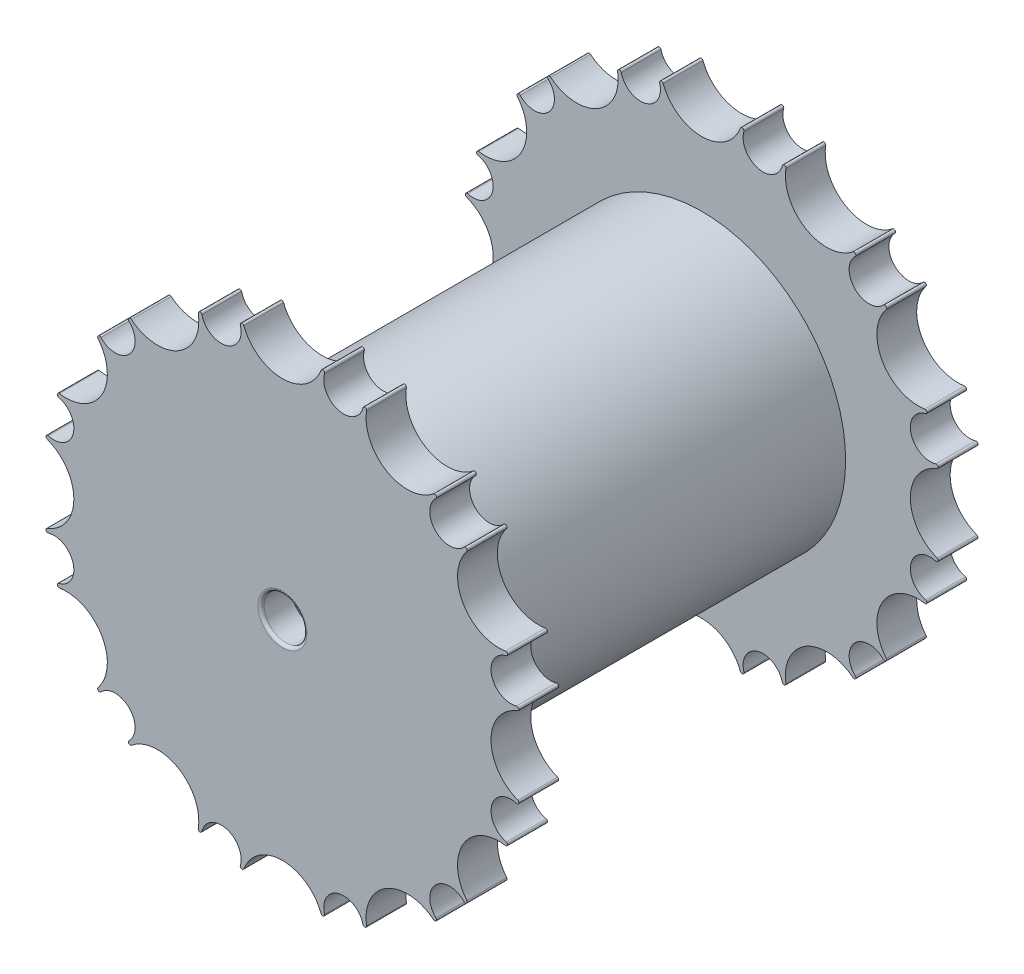
SolidWorks part; units mm, degrees
ref_plane "Front Plane" through (0, 0, 0) normal (0, 0, 1) x (1, 0, 0)
ref_plane "Top Plane" through (0, 0, 0) normal (0, 1, 0) x (1, 0, 0)
ref_plane "Right Plane" through (0, 0, 0) normal (1, 0, 0) x (0, 0, -1)
sketch "Sketch1" plane through (0, 0, 0) normal (0, 0, 1) x (1, 0, 0)
  line L1 (5, -18.6603) -> (13.6603, -13.6603)
  line L2 (13.6603, -13.6603) -> (18.6603, -5)
  line L3 (18.6603, -5) -> (18.6603, 5)
  line L4 (18.6603, 5) -> (13.6603, 13.6603)
  line L5 (13.6603, 13.6603) -> (5, 18.6603)
  line L6 (5, 18.6603) -> (-5, 18.6603)
  line L7 (-5, 18.6603) -> (-13.6603, 13.6603)
  line L8 (-13.6603, 13.6603) -> (-18.6603, 5)
  line L9 (-18.6603, 5) -> (-18.6603, -5)
  line L10 (-18.6603, -5) -> (-13.6603, -13.6603)
  line L11 (-13.6603, -13.6603) -> (-5, -18.6603)
  line L12 (-5, -18.6603) -> (5, -18.6603)
  circle A0 centre (0, 0) radius 18.6603 construction
  circle A1 centre (-5, 18.6603) radius 1.5 construction
  circle A2 centre (5, 18.6603) radius 1.5 construction
  circle A3 centre (-5, 18.6603) radius 1.625
  circle A4 centre (5, 18.6603) radius 1.625
  circle A5 centre (0, 20.4103) radius 3.375 construction
  arc A6 (-3.4408, 19.1179) -> (-3.1557, 19.2136) centre (-3.2964, 19.1603) cw
  arc A7 (3.1557, 19.2136) -> (3.4408, 19.1179) centre (3.2964, 19.1603) cw
  point P1 (0, 18.6603)
  dimension "D2" = 3
  dimension "D5" = 6.75
  dimension "D1" = 10
  dimension "D6" = 1.75
  dimension "D7" = 0.5
  dimension "D3" = 0.125
  dimension "D4" = 0.125
sketch "Sketch10" plane through (0, 0, 0) normal (0, 0, 1) x (1, 0, 0)
  line L2 (-5, -18.6603) -> (5, -18.6603) construction
  line L14 (-3.375, -18.6603) -> (-2.8858, -18.6603)
  circle A0 centre (5, 18.6603) radius 1.625 construction
  arc A1 (3.4408, 19.1179) -> (3.1557, 19.2136) centre (3.2964, 19.1603) ccw construction
  circle A2 centre (0, 20.4103) radius 3.375 construction
  arc A3 (-3.1557, 19.2136) -> (-3.4408, 19.1179) centre (-3.2964, 19.1603) ccw construction
  circle A4 centre (-5, 18.6603) radius 1.625 construction
  arc A5 (3.4408, 19.1179) -> (6.5791, 18.277) centre (5, 18.6603) ccw
  arc A6 (3.4408, 19.1179) -> (3.1557, 19.2136) centre (3.2964, 19.1603) ccw
  arc A7 (-3.1557, 19.2136) -> (3.1557, 19.2136) centre (0, 20.4103) ccw
  arc A8 (-3.1557, 19.2136) -> (-3.4408, 19.1179) centre (-3.2964, 19.1603) ccw
  arc A9 (-6.4073, 17.8478) -> (-3.4408, 19.1179) centre (-5, 18.6603) ccw
  circle A12 centre (0, 0) radius 12.5
  arc A14 (3.375, 18.6603) -> (6.5791, 18.277) centre (5, 18.6603) ccw
  arc A15 (6.8739, 18.2173) -> (6.5791, 18.277) centre (6.7254, 18.2415) ccw
  arc A16 (6.8739, 18.2173) -> (12.3397, 15.0616) centre (10.2051, 17.6758) ccw
  arc A17 (12.5387, 14.8362) -> (12.3397, 15.0616) centre (12.4349, 14.9451) ccw
  arc A18 (12.5387, 14.8362) -> (14.8362, 12.5387) centre (13.6603, 13.6603) ccw
  arc A19 (12.253, 14.4728) -> (14.8362, 12.5387) centre (13.6603, 13.6603) ccw
  arc A20 (15.0616, 12.3397) -> (14.8362, 12.5387) centre (14.9451, 12.4349) ccw
  arc A21 (15.0616, 12.3397) -> (18.2173, 6.8739) centre (17.6758, 10.2051) ccw
  arc A22 (18.277, 6.5791) -> (18.2173, 6.8739) centre (18.2415, 6.7254) ccw
  arc A23 (18.277, 6.5791) -> (19.1179, 3.4408) centre (18.6603, 5) ccw
  arc A24 (17.8478, 6.4073) -> (19.1179, 3.4408) centre (18.6603, 5) ccw
  arc A25 (19.2136, 3.1557) -> (19.1179, 3.4408) centre (19.1603, 3.2964) ccw
  arc A26 (19.2136, 3.1557) -> (19.2136, -3.1557) centre (20.4103, 0) ccw
  arc A27 (19.1179, -3.4408) -> (19.2136, -3.1557) centre (19.1603, -3.2964) ccw
  arc A28 (19.1179, -3.4408) -> (18.277, -6.5791) centre (18.6603, -5) ccw
  arc A29 (18.6603, -3.375) -> (18.277, -6.5791) centre (18.6603, -5) ccw
  arc A30 (18.2173, -6.8739) -> (18.277, -6.5791) centre (18.2415, -6.7254) ccw
  arc A31 (18.2173, -6.8739) -> (15.0616, -12.3397) centre (17.6758, -10.2051) ccw
  arc A32 (14.8362, -12.5387) -> (15.0616, -12.3397) centre (14.9451, -12.4349) ccw
  arc A33 (14.8362, -12.5387) -> (12.5387, -14.8362) centre (13.6603, -13.6603) ccw
  arc A34 (14.4728, -12.253) -> (12.5387, -14.8362) centre (13.6603, -13.6603) ccw
  arc A35 (12.3397, -15.0616) -> (12.5387, -14.8362) centre (12.4349, -14.9451) ccw
  arc A36 (12.3397, -15.0616) -> (6.8739, -18.2173) centre (10.2051, -17.6758) ccw
  arc A37 (6.5791, -18.277) -> (6.8739, -18.2173) centre (6.7254, -18.2415) ccw
  arc A38 (6.5791, -18.277) -> (3.4408, -19.1179) centre (5, -18.6603) ccw
  arc A39 (6.4073, -17.8478) -> (3.4408, -19.1179) centre (5, -18.6603) ccw
  arc A40 (3.1557, -19.2136) -> (3.4408, -19.1179) centre (3.2964, -19.1603) ccw
  arc A41 (3.1557, -19.2136) -> (-3.1557, -19.2136) centre (0, -20.4103) ccw
  arc A42 (-3.4408, -19.1179) -> (-3.1557, -19.2136) centre (-3.2964, -19.1603) ccw
  arc A43 (-3.4408, -19.1179) -> (-6.5791, -18.277) centre (-5, -18.6603) ccw
  arc A44 (-3.375, -18.6603) -> (-6.5791, -18.277) centre (-5, -18.6603) ccw
  arc A45 (-6.8739, -18.2173) -> (-6.5791, -18.277) centre (-6.7254, -18.2415) ccw
  arc A46 (-6.8739, -18.2173) -> (-12.3397, -15.0616) centre (-10.2051, -17.6758) ccw
  arc A47 (-12.5387, -14.8362) -> (-12.3397, -15.0616) centre (-12.4349, -14.9451) ccw
  arc A48 (-12.5387, -14.8362) -> (-14.8362, -12.5387) centre (-13.6603, -13.6603) ccw
  arc A49 (-12.253, -14.4728) -> (-14.8362, -12.5387) centre (-13.6603, -13.6603) ccw
  arc A50 (-15.0616, -12.3397) -> (-14.8362, -12.5387) centre (-14.9451, -12.4349) ccw
  arc A51 (-15.0616, -12.3397) -> (-18.2173, -6.8739) centre (-17.6758, -10.2051) ccw
  arc A52 (-18.277, -6.5791) -> (-18.2173, -6.8739) centre (-18.2415, -6.7254) ccw
  arc A53 (-18.277, -6.5791) -> (-19.1179, -3.4408) centre (-18.6603, -5) ccw
  arc A54 (-17.8478, -6.4073) -> (-19.1179, -3.4408) centre (-18.6603, -5) ccw
  arc A55 (-19.2136, -3.1557) -> (-19.1179, -3.4408) centre (-19.1603, -3.2964) ccw
  arc A56 (-19.2136, -3.1557) -> (-19.2136, 3.1557) centre (-20.4103, 0) ccw
  arc A57 (-19.1179, 3.4408) -> (-19.2136, 3.1557) centre (-19.1603, 3.2964) ccw
  arc A58 (-19.1179, 3.4408) -> (-18.277, 6.5791) centre (-18.6603, 5) ccw
  arc A59 (-18.6603, 3.375) -> (-18.277, 6.5791) centre (-18.6603, 5) ccw
  arc A60 (-18.2173, 6.8739) -> (-18.277, 6.5791) centre (-18.2415, 6.7254) ccw
  arc A61 (-18.2173, 6.8739) -> (-15.0616, 12.3397) centre (-17.6758, 10.2051) ccw
  arc A62 (-14.8362, 12.5387) -> (-15.0616, 12.3397) centre (-14.9451, 12.4349) ccw
  arc A63 (-14.8362, 12.5387) -> (-12.5387, 14.8362) centre (-13.6603, 13.6603) ccw
  arc A64 (-14.4728, 12.253) -> (-12.5387, 14.8362) centre (-13.6603, 13.6603) ccw
  arc A65 (-12.3397, 15.0616) -> (-12.5387, 14.8362) centre (-12.4349, 14.9451) ccw
  arc A66 (-12.3397, 15.0616) -> (-6.8739, 18.2173) centre (-10.2051, 17.6758) ccw
  arc A67 (-6.5791, 18.277) -> (-6.8739, 18.2173) centre (-6.7254, 18.2415) ccw
  arc A68 (-6.5791, 18.277) -> (-3.4408, 19.1179) centre (-5, 18.6603) ccw
  point P162 (0, 0)
  dimension "D2" = 25
  dimension "D1" = 12
sketch "Sketch2" plane through (0, 0, 0) normal (0, 0, 1) x (1, 0, 0)
  line L0 (-10, 37.3205) -> (0, 0) construction
  line L1 (0, 0) -> (10, 37.3205) construction
  arc A5 (6.8815, 38.2358) -> (6.3115, 38.4272) centre (6.5928, 38.3205) ccw
  arc A6 (6.8815, 38.2358) -> (9.1588, 34.1812) centre (10, 37.3205) ccw
  arc A7 (-6.3115, 38.4272) -> (6.3115, 38.4272) centre (0, 40.8205) ccw
  arc A8 (-6.3115, 38.4272) -> (-6.8815, 38.2358) centre (-6.5928, 38.3205) ccw
  arc A9 (-9.1588, 34.1812) -> (-6.8815, 38.2358) centre (-10, 37.3205) ccw
  arc A10 (9.1588, 34.1812) -> (13.1583, 36.5539) centre (10, 37.3205) ccw
  arc A11 (13.7477, 36.4347) -> (13.1583, 36.5539) centre (13.4507, 36.4829) ccw
  arc A12 (13.7477, 36.4347) -> (24.6795, 30.1232) centre (20.4103, 35.3516) ccw
  arc A13 (25.0775, 29.6724) -> (24.6795, 30.1232) centre (24.8698, 29.8901) ccw
  arc A14 (25.0775, 29.6724) -> (25.0224, 25.0224) centre (27.3205, 27.3205) ccw
  arc A15 (25.0224, 25.0224) -> (29.6724, 25.0775) centre (27.3205, 27.3205) ccw
  arc A16 (30.1232, 24.6795) -> (29.6724, 25.0775) centre (29.8901, 24.8698) ccw
  arc A17 (30.1232, 24.6795) -> (36.4347, 13.7477) centre (35.3516, 20.4103) ccw
  arc A18 (36.5539, 13.1583) -> (36.4347, 13.7477) centre (36.4829, 13.4507) ccw
  arc A19 (36.5539, 13.1583) -> (34.1812, 9.1588) centre (37.3205, 10) ccw
  arc A20 (34.1812, 9.1588) -> (38.2358, 6.8815) centre (37.3205, 10) ccw
  arc A21 (38.4272, 6.3115) -> (38.2358, 6.8815) centre (38.3205, 6.5928) ccw
  arc A22 (38.4272, 6.3115) -> (38.4272, -6.3115) centre (40.8205, 0) ccw
  arc A23 (38.2358, -6.8815) -> (38.4272, -6.3115) centre (38.3205, -6.5928) ccw
  arc A24 (38.2358, -6.8815) -> (34.1812, -9.1588) centre (37.3205, -10) ccw
  arc A25 (34.1812, -9.1588) -> (36.5539, -13.1583) centre (37.3205, -10) ccw
  arc A26 (36.4347, -13.7477) -> (36.5539, -13.1583) centre (36.4829, -13.4507) ccw
  arc A27 (36.4347, -13.7477) -> (30.1232, -24.6795) centre (35.3516, -20.4103) ccw
  arc A28 (29.6724, -25.0775) -> (30.1232, -24.6795) centre (29.8901, -24.8698) ccw
  arc A29 (29.6724, -25.0775) -> (25.0224, -25.0224) centre (27.3205, -27.3205) ccw
  arc A30 (25.0224, -25.0224) -> (25.0775, -29.6724) centre (27.3205, -27.3205) ccw
  arc A31 (24.6795, -30.1232) -> (25.0775, -29.6724) centre (24.8698, -29.8901) ccw
  arc A32 (24.6795, -30.1232) -> (13.7477, -36.4347) centre (20.4103, -35.3516) ccw
  arc A33 (13.1583, -36.5539) -> (13.7477, -36.4347) centre (13.4507, -36.4829) ccw
  arc A34 (13.1583, -36.5539) -> (9.1588, -34.1812) centre (10, -37.3205) ccw
  arc A35 (9.1588, -34.1812) -> (6.8815, -38.2358) centre (10, -37.3205) ccw
  arc A36 (6.3115, -38.4272) -> (6.8815, -38.2358) centre (6.5928, -38.3205) ccw
  arc A37 (6.3115, -38.4272) -> (-6.3115, -38.4272) centre (0, -40.8205) ccw
  arc A38 (-6.8815, -38.2358) -> (-6.3115, -38.4272) centre (-6.5928, -38.3205) ccw
  arc A39 (-6.8815, -38.2358) -> (-9.1588, -34.1812) centre (-10, -37.3205) ccw
  arc A40 (-9.1588, -34.1812) -> (-13.1583, -36.5539) centre (-10, -37.3205) ccw
  arc A41 (-13.7477, -36.4347) -> (-13.1583, -36.5539) centre (-13.4507, -36.4829) ccw
  arc A42 (-13.7477, -36.4347) -> (-24.6795, -30.1232) centre (-20.4103, -35.3516) ccw
  arc A43 (-25.0775, -29.6724) -> (-24.6795, -30.1232) centre (-24.8698, -29.8901) ccw
  arc A44 (-25.0775, -29.6724) -> (-25.0224, -25.0224) centre (-27.3205, -27.3205) ccw
  arc A45 (-25.0224, -25.0224) -> (-29.6724, -25.0775) centre (-27.3205, -27.3205) ccw
  arc A46 (-30.1232, -24.6795) -> (-29.6724, -25.0775) centre (-29.8901, -24.8698) ccw
  arc A47 (-30.1232, -24.6795) -> (-36.4347, -13.7477) centre (-35.3516, -20.4103) ccw
  arc A48 (-36.5539, -13.1583) -> (-36.4347, -13.7477) centre (-36.4829, -13.4507) ccw
  arc A49 (-36.5539, -13.1583) -> (-34.1812, -9.1588) centre (-37.3205, -10) ccw
  arc A50 (-34.1812, -9.1588) -> (-38.2358, -6.8815) centre (-37.3205, -10) ccw
  arc A51 (-38.4272, -6.3115) -> (-38.2358, -6.8815) centre (-38.3205, -6.5928) ccw
  arc A52 (-38.4272, -6.3115) -> (-38.4272, 6.3115) centre (-40.8205, 0) ccw
  arc A53 (-38.2358, 6.8815) -> (-38.4272, 6.3115) centre (-38.3205, 6.5928) ccw
  arc A54 (-38.2358, 6.8815) -> (-34.1812, 9.1588) centre (-37.3205, 10) ccw
  arc A55 (-34.1812, 9.1588) -> (-36.5539, 13.1583) centre (-37.3205, 10) ccw
  arc A56 (-36.4347, 13.7477) -> (-36.5539, 13.1583) centre (-36.4829, 13.4507) ccw
  arc A57 (-36.4347, 13.7477) -> (-30.1232, 24.6795) centre (-35.3516, 20.4103) ccw
  arc A58 (-29.6724, 25.0775) -> (-30.1232, 24.6795) centre (-29.8901, 24.8698) ccw
  arc A59 (-29.6724, 25.0775) -> (-25.0224, 25.0224) centre (-27.3205, 27.3205) ccw
  arc A60 (-25.0224, 25.0224) -> (-25.0775, 29.6724) centre (-27.3205, 27.3205) ccw
  arc A61 (-24.6795, 30.1232) -> (-25.0775, 29.6724) centre (-24.8698, 29.8901) ccw
  arc A62 (-24.6795, 30.1232) -> (-13.7477, 36.4347) centre (-20.4103, 35.3516) ccw
  arc A63 (-13.1583, 36.5539) -> (-13.7477, 36.4347) centre (-13.4507, 36.4829) ccw
  arc A64 (-13.1583, 36.5539) -> (-9.1588, 34.1812) centre (-10, 37.3205) ccw
  circle A65 centre (0, 0) radius 30
  point P139 (0, 0)
  dimension "D2" = 60
  dimension "D3" = 6.75
  dimension "D1" = 12
sketch "Sketch4" plane through (0, 0, 0) normal (0, 0, 1) x (1, 0, 0)
  arc A62 (-24.6795, 30.1232) -> (-25.0775, 29.6724) centre (-24.8698, 29.8901) ccw
  arc A63 (-24.6795, 30.1232) -> (-13.7477, 36.4347) centre (-20.4103, 35.3516) ccw
  arc A64 (-13.1583, 36.5539) -> (-13.7477, 36.4347) centre (-13.4507, 36.4829) ccw
  arc A65 (-13.1583, 36.5539) -> (-9.1588, 34.1812) centre (-10, 37.3205) ccw
  arc A66 (-9.1588, 34.1812) -> (-6.8815, 38.2358) centre (-10, 37.3205) ccw
  arc A67 (-6.3115, 38.4272) -> (-6.8815, 38.2358) centre (-6.5928, 38.3205) ccw
  arc A68 (-6.3115, 38.4272) -> (6.3115, 38.4272) centre (0, 40.8205) ccw
  arc A69 (6.8815, 38.2358) -> (6.3115, 38.4272) centre (6.5928, 38.3205) ccw
  arc A70 (6.8815, 38.2358) -> (9.1588, 34.1812) centre (10, 37.3205) ccw
  arc A71 (9.1588, 34.1812) -> (13.1583, 36.5539) centre (10, 37.3205) ccw
  arc A72 (13.7477, 36.4347) -> (13.1583, 36.5539) centre (13.4507, 36.4829) ccw
  arc A73 (13.7477, 36.4347) -> (24.6795, 30.1232) centre (20.4103, 35.3516) ccw
  arc A74 (25.0775, 29.6724) -> (24.6795, 30.1232) centre (24.8698, 29.8901) ccw
  arc A75 (25.0775, 29.6724) -> (25.0224, 25.0224) centre (27.3205, 27.3205) ccw
  arc A76 (25.0224, 25.0224) -> (29.6724, 25.0775) centre (27.3205, 27.3205) ccw
  arc A77 (30.1232, 24.6795) -> (29.6724, 25.0775) centre (29.8901, 24.8698) ccw
  arc A78 (30.1232, 24.6795) -> (36.4347, 13.7477) centre (35.3516, 20.4103) ccw
  arc A79 (36.5539, 13.1583) -> (36.4347, 13.7477) centre (36.4829, 13.4507) ccw
  arc A80 (36.5539, 13.1583) -> (34.1812, 9.1588) centre (37.3205, 10) ccw
  arc A81 (34.1812, 9.1588) -> (38.2358, 6.8815) centre (37.3205, 10) ccw
  arc A82 (38.4272, 6.3115) -> (38.2358, 6.8815) centre (38.3205, 6.5928) ccw
  arc A83 (38.4272, 6.3115) -> (38.4272, -6.3115) centre (40.8205, 0) ccw
  arc A84 (38.2358, -6.8815) -> (38.4272, -6.3115) centre (38.3205, -6.5928) ccw
  arc A85 (38.2358, -6.8815) -> (34.1812, -9.1588) centre (37.3205, -10) ccw
  arc A86 (34.1812, -9.1588) -> (36.5539, -13.1583) centre (37.3205, -10) ccw
  arc A87 (36.4347, -13.7477) -> (36.5539, -13.1583) centre (36.4829, -13.4507) ccw
  arc A88 (36.4347, -13.7477) -> (30.1232, -24.6795) centre (35.3516, -20.4103) ccw
  arc A89 (29.6724, -25.0775) -> (30.1232, -24.6795) centre (29.8901, -24.8698) ccw
  arc A90 (29.6724, -25.0775) -> (25.0224, -25.0224) centre (27.3205, -27.3205) ccw
  arc A91 (25.0224, -25.0224) -> (25.0775, -29.6724) centre (27.3205, -27.3205) ccw
  arc A92 (24.6795, -30.1232) -> (25.0775, -29.6724) centre (24.8698, -29.8901) ccw
  arc A93 (24.6795, -30.1232) -> (13.7477, -36.4347) centre (20.4103, -35.3516) ccw
  arc A94 (13.1583, -36.5539) -> (13.7477, -36.4347) centre (13.4507, -36.4829) ccw
  arc A95 (13.1583, -36.5539) -> (9.1588, -34.1812) centre (10, -37.3205) ccw
  arc A96 (9.1588, -34.1812) -> (6.8815, -38.2358) centre (10, -37.3205) ccw
  arc A97 (6.3115, -38.4272) -> (6.8815, -38.2358) centre (6.5928, -38.3205) ccw
  arc A98 (6.3115, -38.4272) -> (-6.3115, -38.4272) centre (0, -40.8205) ccw
  arc A99 (-6.8815, -38.2358) -> (-6.3115, -38.4272) centre (-6.5928, -38.3205) ccw
  arc A100 (-6.8815, -38.2358) -> (-9.1588, -34.1812) centre (-10, -37.3205) ccw
  arc A101 (-9.1588, -34.1812) -> (-13.1583, -36.5539) centre (-10, -37.3205) ccw
  arc A102 (-13.7477, -36.4347) -> (-13.1583, -36.5539) centre (-13.4507, -36.4829) ccw
  arc A103 (-13.7477, -36.4347) -> (-24.6795, -30.1232) centre (-20.4103, -35.3516) ccw
  arc A104 (-25.0775, -29.6724) -> (-24.6795, -30.1232) centre (-24.8698, -29.8901) ccw
  arc A105 (-25.0775, -29.6724) -> (-25.0224, -25.0224) centre (-27.3205, -27.3205) ccw
  arc A106 (-25.0224, -25.0224) -> (-29.6724, -25.0775) centre (-27.3205, -27.3205) ccw
  arc A107 (-30.1232, -24.6795) -> (-29.6724, -25.0775) centre (-29.8901, -24.8698) ccw
  arc A108 (-30.1232, -24.6795) -> (-36.4347, -13.7477) centre (-35.3516, -20.4103) ccw
  arc A109 (-36.5539, -13.1583) -> (-36.4347, -13.7477) centre (-36.4829, -13.4507) ccw
  arc A110 (-36.5539, -13.1583) -> (-34.1812, -9.1588) centre (-37.3205, -10) ccw
  arc A111 (-34.1812, -9.1588) -> (-38.2358, -6.8815) centre (-37.3205, -10) ccw
  arc A112 (-38.4272, -6.3115) -> (-38.2358, -6.8815) centre (-38.3205, -6.5928) ccw
  arc A113 (-38.4272, -6.3115) -> (-38.4272, 6.3115) centre (-40.8205, 0) ccw
  arc A114 (-38.2358, 6.8815) -> (-38.4272, 6.3115) centre (-38.3205, 6.5928) ccw
  arc A115 (-38.2358, 6.8815) -> (-34.1812, 9.1588) centre (-37.3205, 10) ccw
  arc A116 (-34.1812, 9.1588) -> (-36.5539, 13.1583) centre (-37.3205, 10) ccw
  arc A117 (-36.4347, 13.7477) -> (-36.5539, 13.1583) centre (-36.4829, 13.4507) ccw
  arc A118 (-36.4347, 13.7477) -> (-30.1232, 24.6795) centre (-35.3516, 20.4103) ccw
  arc A119 (-29.6724, 25.0775) -> (-30.1232, 24.6795) centre (-29.8901, 24.8698) ccw
  arc A120 (-29.6724, 25.0775) -> (-25.0224, 25.0224) centre (-27.3205, 27.3205) ccw
  arc A121 (-25.0224, 25.0224) -> (-25.0775, 29.6724) centre (-27.3205, 27.3205) ccw
  arc A122 (-24.6795, 30.1232) -> (-25.0775, 29.6724) centre (-24.8698, 29.8901) ccw
  arc A123 (-24.6795, 30.1232) -> (-13.7477, 36.4347) centre (-20.4103, 35.3516) ccw
  arc A124 (-13.1583, 36.5539) -> (-13.7477, 36.4347) centre (-13.4507, 36.4829) ccw
  arc A125 (-13.1583, 36.5539) -> (-9.1588, 34.1812) centre (-10, 37.3205) ccw
  arc A126 (-9.1588, 34.1812) -> (-6.8815, 38.2358) centre (-10, 37.3205) ccw
  arc A127 (-6.3115, 38.4272) -> (-6.8815, 38.2358) centre (-6.5928, 38.3205) ccw
  arc A128 (-6.3115, 38.4272) -> (6.3115, 38.4272) centre (0, 40.8205) ccw
  arc A129 (6.8815, 38.2358) -> (6.3115, 38.4272) centre (6.5928, 38.3205) ccw
  arc A130 (6.8815, 38.2358) -> (9.1588, 34.1812) centre (10, 37.3205) ccw
  arc A131 (9.1588, 34.1812) -> (13.1583, 36.5539) centre (10, 37.3205) ccw
  arc A132 (13.7477, 36.4347) -> (13.1583, 36.5539) centre (13.4507, 36.4829) ccw
  arc A133 (13.7477, 36.4347) -> (24.6795, 30.1232) centre (20.4103, 35.3516) ccw
  arc A134 (25.0775, 29.6724) -> (24.6795, 30.1232) centre (24.8698, 29.8901) ccw
  arc A135 (25.0775, 29.6724) -> (25.0224, 25.0224) centre (27.3205, 27.3205) ccw
  arc A136 (25.0224, 25.0224) -> (29.6724, 25.0775) centre (27.3205, 27.3205) ccw
  arc A137 (30.1232, 24.6795) -> (29.6724, 25.0775) centre (29.8901, 24.8698) ccw
  arc A138 (30.1232, 24.6795) -> (36.4347, 13.7477) centre (35.3516, 20.4103) ccw
  arc A139 (36.5539, 13.1583) -> (36.4347, 13.7477) centre (36.4829, 13.4507) ccw
  arc A140 (36.5539, 13.1583) -> (34.1812, 9.1588) centre (37.3205, 10) ccw
  arc A141 (34.1812, 9.1588) -> (38.2358, 6.8815) centre (37.3205, 10) ccw
  arc A142 (38.4272, 6.3115) -> (38.2358, 6.8815) centre (38.3205, 6.5928) ccw
  arc A143 (38.4272, 6.3115) -> (38.4272, -6.3115) centre (40.8205, 0) ccw
  arc A144 (38.2358, -6.8815) -> (38.4272, -6.3115) centre (38.3205, -6.5928) ccw
  arc A145 (38.2358, -6.8815) -> (34.1812, -9.1588) centre (37.3205, -10) ccw
  arc A146 (34.1812, -9.1588) -> (36.5539, -13.1583) centre (37.3205, -10) ccw
  arc A147 (36.4347, -13.7477) -> (36.5539, -13.1583) centre (36.4829, -13.4507) ccw
  arc A148 (36.4347, -13.7477) -> (30.1232, -24.6795) centre (35.3516, -20.4103) ccw
  arc A149 (29.6724, -25.0775) -> (30.1232, -24.6795) centre (29.8901, -24.8698) ccw
  arc A150 (29.6724, -25.0775) -> (25.0224, -25.0224) centre (27.3205, -27.3205) ccw
  arc A151 (25.0224, -25.0224) -> (25.0775, -29.6724) centre (27.3205, -27.3205) ccw
  arc A152 (24.6795, -30.1232) -> (25.0775, -29.6724) centre (24.8698, -29.8901) ccw
  arc A153 (24.6795, -30.1232) -> (13.7477, -36.4347) centre (20.4103, -35.3516) ccw
  arc A154 (13.1583, -36.5539) -> (13.7477, -36.4347) centre (13.4507, -36.4829) ccw
  arc A155 (13.1583, -36.5539) -> (9.1588, -34.1812) centre (10, -37.3205) ccw
  arc A156 (9.1588, -34.1812) -> (6.8815, -38.2358) centre (10, -37.3205) ccw
  arc A157 (6.3115, -38.4272) -> (6.8815, -38.2358) centre (6.5928, -38.3205) ccw
  arc A158 (6.3115, -38.4272) -> (-6.3115, -38.4272) centre (0, -40.8205) ccw
  arc A159 (-6.8815, -38.2358) -> (-6.3115, -38.4272) centre (-6.5928, -38.3205) ccw
  arc A160 (-6.8815, -38.2358) -> (-9.1588, -34.1812) centre (-10, -37.3205) ccw
  arc A161 (-9.1588, -34.1812) -> (-13.1583, -36.5539) centre (-10, -37.3205) ccw
  arc A162 (-13.7477, -36.4347) -> (-13.1583, -36.5539) centre (-13.4507, -36.4829) ccw
  arc A163 (-13.7477, -36.4347) -> (-24.6795, -30.1232) centre (-20.4103, -35.3516) ccw
  arc A164 (-25.0775, -29.6724) -> (-24.6795, -30.1232) centre (-24.8698, -29.8901) ccw
  arc A165 (-25.0775, -29.6724) -> (-25.0224, -25.0224) centre (-27.3205, -27.3205) ccw
  arc A166 (-25.0224, -25.0224) -> (-29.6724, -25.0775) centre (-27.3205, -27.3205) ccw
  arc A167 (-30.1232, -24.6795) -> (-29.6724, -25.0775) centre (-29.8901, -24.8698) ccw
  arc A168 (-30.1232, -24.6795) -> (-36.4347, -13.7477) centre (-35.3516, -20.4103) ccw
  arc A169 (-36.5539, -13.1583) -> (-36.4347, -13.7477) centre (-36.4829, -13.4507) ccw
  arc A170 (-36.5539, -13.1583) -> (-34.1812, -9.1588) centre (-37.3205, -10) ccw
  arc A171 (-34.1812, -9.1588) -> (-38.2358, -6.8815) centre (-37.3205, -10) ccw
  arc A172 (-38.4272, -6.3115) -> (-38.2358, -6.8815) centre (-38.3205, -6.5928) ccw
  arc A173 (-38.4272, -6.3115) -> (-38.4272, 6.3115) centre (-40.8205, 0) ccw
  arc A174 (-38.2358, 6.8815) -> (-38.4272, 6.3115) centre (-38.3205, 6.5928) ccw
  arc A175 (-38.2358, 6.8815) -> (-34.1812, 9.1588) centre (-37.3205, 10) ccw
  arc A176 (-34.1812, 9.1588) -> (-36.5539, 13.1583) centre (-37.3205, 10) ccw
  arc A177 (-36.4347, 13.7477) -> (-36.5539, 13.1583) centre (-36.4829, 13.4507) ccw
  arc A178 (-36.4347, 13.7477) -> (-30.1232, 24.6795) centre (-35.3516, 20.4103) ccw
  arc A179 (-29.6724, 25.0775) -> (-30.1232, 24.6795) centre (-29.8901, 24.8698) ccw
  arc A180 (-29.6724, 25.0775) -> (-25.0224, 25.0224) centre (-27.3205, 27.3205) ccw
  arc A181 (-25.0224, 25.0224) -> (-25.0775, 29.6724) centre (-27.3205, 27.3205) ccw
  dimension "D2" = 0
extrude "Boss-Extrude1" add sketch "Sketch4" along normal mid plane 6.5
sketch "Sketch5" plane through (0, 0, 0) normal (0, 0, 1) x (1, 0, 0)
  circle A0 centre (0, 0) radius 10
  circle A1 centre (0, 0) radius 20
  dimension "D1" = 20
  dimension "D2" = 10
extrude "Boss-Extrude2" add sketch "Sketch5" along normal mid plane 2 separate body
sketch "Sketch6" plane through (0, 0, 1) normal (0, 0, 1) x (1, 0, 0)
  line L0 (0, 29.9906) -> (0, 19.9906) construction
  line L1 (0.75, 29.9906) -> (0.75, 19.9906)
  line L2 (-0.75, 29.9906) -> (-0.75, 19.9906)
  line L3 (25.5976, 15.6448) -> (16.9374, 10.6448)
  line L4 (26.3476, 14.3458) -> (17.6874, 9.3458)
  line L5 (25.9726, 14.9953) -> (17.3124, 9.9953) construction
  line L6 (26.3476, -14.3458) -> (17.6874, -9.3458)
  line L7 (25.5976, -15.6448) -> (16.9374, -10.6448)
  line L8 (25.9726, -14.9953) -> (17.3124, -9.9953) construction
  line L9 (0.75, -29.9906) -> (0.75, -19.9906)
  line L10 (-0.75, -29.9906) -> (-0.75, -19.9906)
  line L11 (0, -29.9906) -> (0, -19.9906) construction
  line L12 (-25.5976, -15.6448) -> (-16.9374, -10.6448)
  line L13 (-26.3476, -14.3458) -> (-17.6874, -9.3458)
  line L14 (-25.9726, -14.9953) -> (-17.3124, -9.9953) construction
  line L15 (-26.3476, 14.3458) -> (-17.6874, 9.3458)
  line L16 (-25.5976, 15.6448) -> (-16.9374, 10.6448)
  line L17 (-25.9726, 14.9953) -> (-17.3124, 9.9953) construction
  arc A0 (0.75, 29.9906) -> (-0.75, 29.9906) centre (0, 29.9906) ccw
  arc A1 (-0.75, 19.9906) -> (0.75, 19.9906) centre (0, 19.9906) ccw
  circle A2 centre (0, 0) radius 30 construction
  arc A3 (26.3476, 14.3458) -> (25.5976, 15.6448) centre (25.9726, 14.9953) ccw
  arc A4 (16.9374, 10.6448) -> (17.6874, 9.3458) centre (17.3124, 9.9953) ccw
  arc A5 (25.5976, -15.6448) -> (26.3476, -14.3458) centre (25.9726, -14.9953) ccw
  arc A6 (17.6874, -9.3458) -> (16.9374, -10.6448) centre (17.3124, -9.9953) ccw
  arc A7 (-0.75, -29.9906) -> (0.75, -29.9906) centre (0, -29.9906) ccw
  arc A8 (0.75, -19.9906) -> (-0.75, -19.9906) centre (0, -19.9906) ccw
  arc A9 (-26.3476, -14.3458) -> (-25.5976, -15.6448) centre (-25.9726, -14.9953) ccw
  arc A10 (-16.9374, -10.6448) -> (-17.6874, -9.3458) centre (-17.3124, -9.9953) ccw
  arc A11 (-25.5976, 15.6448) -> (-26.3476, 14.3458) centre (-25.9726, 14.9953) ccw
  arc A12 (-17.6874, 9.3458) -> (-16.9374, 10.6448) centre (-17.3124, 9.9953) ccw
  point P3 (0, 24.9906)
  point P14 (21.6425, 12.4953)
  point P21 (21.6425, -12.4953)
  point P28 (0, -24.9906)
  point P35 (-21.6425, -12.4953)
  point P42 (-21.6425, 12.4953)
  point P47 (0, 0)
  dimension "D1" = 1.5
  dimension "D2" = 10
  dimension "D3" = 6
extrude "Boss-Extrude3" add sketch "Sketch6" against normal blind 1.5
ref_plane "Plane1" through (0, 0, 34.25) normal (0, 0, 1) x (1, 0, 0)
mirror "Mirror2" about plane through (0, 0, 34.25) normal (0, 0, 1) of bodies 103
sketch "Sketch9" plane through (0, 0, 34.25) normal (0, 0, 1) x (1, 0, 0)
  circle A0 centre (0, 0) radius 23.5
  dimension "D1" = 47
extrude "Boss-Extrude4" add sketch "Sketch9" against normal up to surface and the other way up to surface
sketch "Sketch11" plane through (0, 0, 71.75) normal (0, 0, 1) x (1, 0, 0)
  circle A0 centre (0, 0) radius 3.5
  dimension "D1" = 7
sketch "Sketch12" plane through (0, 0, -3.25) normal (0, 0, -1) x (-1, 0, 0)
  circle A0 centre (0, 0) radius 3.35
  dimension "D1" = 6.7
sketch "Sketch14" plane through (0, 0, -3.25) normal (0, 0, -1) x (-1, 0, 0)
  circle A0 centre (0, 0) radius 3.5
  dimension "D1" = 7
extrude "Cut-Extrude1" cut sketch "Sketch12" against normal blind 5 contours A0
extrude "Cut-Extrude2" cut sketch "Sketch11" against normal blind 5 contours A0
fillet "Fillet1" radius 0.5 2 edges at (-3.35, 0, -3.25) (3.5, 0, 71.75)
sketch "Sketch15" plane through (23.5, 0, 0) normal (1, 0, 0) x (0, 0, -1)
  line L0 (-63.25, 2.8426) -> (-5.25, 2.8426)
  line L1 (-3.25, 23.5) -> (-3.25, -23.5) construction
  line L3 (-65.25, -23.5) -> (-65.25, 23.5) construction
  dimension "D1" = 2
  dimension "D2" = 2
sketch "Sketch16" plane through (23.5, 0, 0) normal (1, 0, 0) x (0, 0, -1)
  line L0 (-71.75, -6.6026) -> (3.25, -6.6026)
  line L1 (-71.75, -6.3115) -> (-71.75, -6.8937) construction
  line L2 (3.25, -6.8937) -> (3.25, -6.3115) construction
